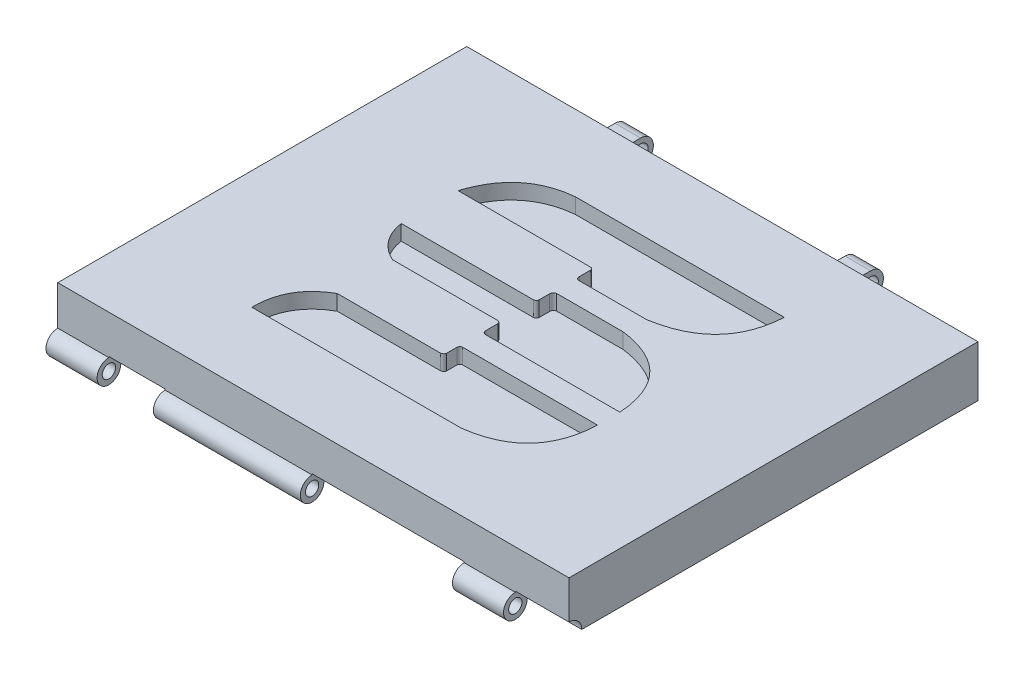
SolidWorks part; units mm, degrees
ref_plane "Front Plane" through (0, 0, 0) normal (0, 0, 1) x (1, 0, 0)
ref_plane "Top Plane" through (0, 0, 0) normal (0, 1, 0) x (1, 0, 0)
ref_plane "Right Plane" through (0, 0, 0) normal (1, 0, 0) x (0, 0, -1)
sketch "Sketch1" plane through (0, 0, 0) normal (0, 1, 0) x (1, 0, 0)
  line L0 (0, 0) -> (254, 0)
  line L1 (254, 0) -> (254, 203.2)
  line L2 (254, 203.2) -> (0, 203.2)
  line L3 (0, 203.2) -> (0, 0)
extrude "Boss-Extrude2" add sketch "Sketch1" along normal blind 12.7
sketch "Sketch2" plane through (0, 0, 0) normal (0, -1, 0) x (-1, 0, 0)
  line L1 (-254, 0) -> (-254, 203.2)
  line L2 (-254, 203.2) -> (0, 203.2)
  line L3 (0, 203.2) -> (0, 0)
  line L4 (0, 0) -> (-254, 0)
  line L6 (-12.7, 12.7) -> (-12.7, 190.5)
  line L7 (-12.7, 12.7) -> (-241.3, 12.7)
  line L8 (-241.3, 12.7) -> (-241.3, 190.5)
  line L9 (-241.3, 190.5) -> (-12.7, 190.5)
extrude "Boss-Extrude3" add sketch "Sketch2" along normal blind 12.7
sketch "Sketch3" plane through (0, 12.7, 0) normal (0, 1, 0) x (1, 0, 0)
  line L0 (-372.7889, 197.1287) -> (560.5445, 197.1287) construction
  line L1 (231.8495, 577.4485) -> (1012.5161, 577.4485) construction
  line L21 (195.367, 165.5458) -> (91.7122, 165.5458)
  line L22 (59.8464, 139.0381) -> (125.3071, 139.0381)
  line L23 (126.9605, 137.7692) -> (126.9605, 132.2725)
  line L24 (128.3037, 130.3712) -> (162.1872, 130.3712)
  line L25 (161.6423, 119.296) -> (128.4978, 119.296)
  line L26 (126.9605, 117.3978) -> (126.9605, 112.1511)
  line L27 (125.4647, 110.7847) -> (59.8464, 110.7847)
  line L28 (73.3174, 93.027) -> (125.4647, 93.027)
  line L29 (126.9605, 91.7488) -> (126.9605, 85.7448)
  line L30 (128.4978, 83.9124) -> (195.367, 83.9124)
  line L31 (195.367, 72.8024) -> (128.3037, 72.8024)
  line L32 (126.9605, 71.2973) -> (126.9605, 66.0747)
  line L33 (125.3071, 64.7692) -> (74.0829, 64.7692)
  line L34 (58.8112, 37.6226) -> (162.7167, 37.6226)
  spline S0 degree 2 poles (195.367, 165.5458) (193.7456, 135.5673) (162.1872, 130.3712) knots 0 0 0 1 1 1
  spline S1 degree 2 poles (91.7122, 165.5458) (67.5392, 163.2352) (59.8464, 139.0381) knots 0 0 0 1 1 1
  spline S2 degree 2 poles (125.3071, 139.0381) (126.7806, 139.1224) (126.9605, 137.7692) knots 0 0 0 1 1 1
  spline S3 degree 2 poles (126.9605, 132.2725) (126.8769, 130.7335) (128.3037, 130.3712) knots 0 0 0 1 1 1
  spline S4 degree 2 poles (128.4978, 119.296) (127.0701, 118.9266) (126.9605, 117.3978) knots 0 0 0 1 1 1
  spline S5 degree 2 poles (126.9605, 112.1511) (126.7438, 110.8994) (125.4647, 110.7847) knots 0 0 0 1 1 1
  spline S6 degree 2 poles (59.8464, 110.7847) (61.8873, 98.3015) (73.3174, 93.027) knots 0 0 0 1 1 1
  spline S7 degree 2 poles (125.4647, 93.027) (126.7117, 92.92) (126.9605, 91.7488) knots 0 0 0 1 1 1
  spline S8 degree 2 poles (126.9605, 85.7448) (127.0243, 84.1959) (128.4978, 83.9124) knots 0 0 0 1 1 1
  spline S9 degree 2 poles (161.6423, 119.296) (193.2226, 115.0134) (195.367, 83.9124) knots 0 0 0 1 1 1
  spline S10 degree 2 poles (128.3037, 72.8024) (127.014, 72.6481) (126.9605, 71.2973) knots 0 0 0 1 1 1
  spline S11 degree 2 poles (126.9605, 66.0747) (126.574, 64.9269) (125.3071, 64.7692) knots 0 0 0 1 1 1
  spline S12 degree 2 poles (74.0829, 64.7692) (58.4795, 55.8847) (58.8112, 37.6226) knots 0 0 0 1 1 1
  spline S13 degree 2 poles (162.7167, 37.6226) (194.1407, 41.706) (195.367, 72.8024) knots 0 0 0 1 1 1
sketch "Sketch5" plane through (0, 0, 0) normal (0, 0, 1) x (1, 0, 0)
  line L0 (254, -12.7) -> (228.6, -12.7)
  line L1 (254, -12.7) -> (0, -12.7) construction
ref_plane "Plane1" through (228.6, 0, 0) normal (1, 0, 0) x (0, 0, -1)
sketch "Sketch6" plane through (228.6, 0, 0) normal (1, 0, 0) x (0, 0, -1)
  circle A0 centre (0, -12.7) radius 6.35
extrude "Cut-Extrude2" cut sketch "Sketch6" against normal blind 52.07
sketch "Sketch7" plane through (0, 0, 0) normal (0, 0, 1) x (1, 0, 0)
  line L0 (0, -12.7) -> (25.4, -12.7)
  line L1 (176.53, -12.7) -> (0, -12.7) construction
ref_plane "Plane2" through (25.4, 0, 0) normal (-1, 0, 0) x (0, 0, 1)
sketch "Sketch8" plane through (25.4, 0, 0) normal (-1, 0, 0) x (0, 0, 1)
  circle A0 centre (0, -12.7) radius 6.35
extrude "Cut-Extrude3" cut sketch "Sketch8" against normal blind 52.07
sketch "Sketch9" plane through (228.6, 0, 0) normal (1, 0, 0) x (0, 0, -1)
  line L0 (0, -6.858) -> (0, -4.7342)
  line L1 (0, 12.7) -> (0, -12.7) construction
  line L2 (0, -4.7342) -> (6.8427, -8.9272)
  line L3 (6.8427, -8.9272) -> (6.8427, -12.7)
  line L4 (203.2, -12.7) -> (0, -12.7) construction
  line L5 (6.8427, -12.7) -> (5.842, -12.7)
  circle A0 centre (0, -12.7) radius 5.842
  circle A1 centre (0, -12.7) radius 3.302
extrude "Boss-Extrude5" add sketch "Sketch9" against normal blind 25.4 contours A0 A1 | A0 L5 L3 L2 L0
sketch "Sketch10" plane through (228.6, 0, 0) normal (1, 0, 0) x (0, 0, -1)
  circle A0 centre (0, -12.7) radius 6.35
extrude "Cut-Extrude4" cut sketch "Sketch10" along normal blind 45.212
sketch "Sketch11" plane through (176.53, 0, 0) normal (1, 0, 0) x (0, 0, -1)
  circle A0 centre (0, -12.7) radius 6.35
extrude "Cut-Extrude5" cut sketch "Sketch11" against normal blind 190.246
sketch "Sketch12" plane through (0, 0, 0) normal (-1, 0, 0) x (0, 0, 1)
  line L0 (0, -6.858) -> (0, -5.7972)
  line L1 (0, 12.7) -> (0, -6.35) construction
  line L2 (0, -5.7972) -> (-4.7292, -7.2686)
  line L3 (-4.7292, -7.2686) -> (-5.7298, -8.7792)
  line L4 (-5.7298, -8.7792) -> (-6.6519, -12.7)
  line L5 (-203.2, -12.7) -> (-6.35, -12.7) construction
  line L6 (-6.6519, -12.7) -> (-5.842, -12.7)
  circle A0 centre (0, -12.7) radius 5.842
  circle A1 centre (0, -12.7) radius 3.302
  arc M2 (-6.35, -12.7) -> (0, -6.35) centre (0, -12.7) cw
extrude "Boss-Extrude6" add sketch "Sketch12" against normal blind 24.13 contours A0 L0 L6 M2 | A0 A1
sketch "Sketch13" plane through (0, 0, 0) normal (0, 0, 1) x (1, 0, 0)
  line L0 (0, -6.858) -> (53.34, -6.858)
ref_plane "Plane3" through (53.34, 0, 0) normal (-1, 0, 0) x (0, 0, 1)
sketch "Sketch15" plane through (228.6, 0, 0) normal (1, 0, 0) x (0, 0, -1)
  circle A0 centre (0, -12.7) radius 6.35
extrude "Cut-Extrude6" cut sketch "Sketch15" against normal blind 1.27
sketch "Sketch17" plane through (203.2, 0, 0) normal (-1, 0, 0) x (0, 0, 1)
  line L0 (0, -6.858) -> (0, -4.987)
  line L1 (0, -4.987) -> (-4.743, -7.1596)
  line L2 (-4.743, -7.1596) -> (-6.563, -10.3545)
  line L3 (-6.563, -10.3545) -> (-6.563, -12.7)
  line L4 (-5.842, -12.7) -> (-203.2, -12.7) construction
  line L5 (-6.563, -12.7) -> (-5.842, -12.7)
  circle A0 centre (0, -12.7) radius 3.302
  circle A1 centre (0, -12.7) radius 5.842
  circle M1 centre (0, -12.7) radius 3.302
  line M2 (0, -6.858) -> (0, -6.35)
  arc M3 (0, -6.35) -> (-6.35, -12.7) centre (0, -12.7) ccw
  line M4 (-6.35, -12.7) -> (-5.842, -12.7)
  arc M5 (-5.842, -12.7) -> (0, -6.858) centre (0, -12.7) ccw
extrude "Boss-Extrude7" add sketch "Sketch17" along normal blind 1.27 contours A1 M2 M3 M4 | A1 M5 M1
sketch "Sketch18" plane through (24.13, 0, 0) normal (1, 0, 0) x (0, 0, -1)
  line L0 (0, -6.858) -> (0, -5.514)
  line L1 (0, -5.514) -> (4.4531, -7.4996)
  line L2 (4.4531, -7.4996) -> (6.3537, -9.9032)
  line L3 (6.3537, -9.9032) -> (6.856, -12.7)
  line L4 (6.856, -12.7) -> (5.842, -12.7)
  circle A0 centre (0, -12.7) radius 3.302
  circle A1 centre (0, -12.7) radius 5.842
  line M1 (5.842, -12.7) -> (6.35, -12.7)
  arc M2 (6.35, -12.7) -> (0, -6.35) centre (0, -12.7) ccw
  line M3 (0, -6.35) -> (0, -6.858)
  arc M4 (0, -6.858) -> (5.842, -12.7) centre (0, -12.7) ccw
  circle M5 centre (0, -12.7) radius 3.302
extrude "Boss-Extrude8" add sketch "Sketch18" along normal blind 1.27 contours A1 M1 M2 M3 | A1 M4 M5
ref_plane "Plane4" through (53.34, 0, 0) normal (-1, 0, 0) x (0, 0, 1)
sketch "Sketch19" plane through (53.34, 0, 0) normal (-1, 0, 0) x (0, 0, 1)
  line L0 (0, -6.858) -> (0, -5.3347)
  line L1 (0, 12.7) -> (0, -6.35) construction
  line L2 (0, -5.3347) -> (-5.2177, -7.6255)
  line L3 (-5.2177, -7.6255) -> (-6.5239, -10.6196)
  line L4 (-6.5239, -10.6196) -> (-6.7248, -12.7)
  line L5 (-203.2, -12.7) -> (-6.35, -12.7) construction
  line L6 (-6.7248, -12.7) -> (-5.842, -12.7)
  circle A0 centre (0, -12.7) radius 3.302
  circle A1 centre (0, -12.7) radius 5.842
extrude "Boss-Extrude9" add sketch "Sketch19" against normal blind 73.025 contours A1 L0 L2 L3 L4 L6 | A1 A0
extrude "Cut-Extrude7" cut sketch "Sketch3" against normal blind 7.62
sketch "Sketch20" plane through (0, 0, -203.2) normal (0, 0, -1) x (-1, 0, 0)
  line L0 (-254, -12.7) -> (-177.8, -12.7)
  line L1 (0, -12.7) -> (-254, -12.7) construction
ref_plane "Plane5" through (177.8, 0, 0) normal (1, 0, 0) x (0, 0, -1)
sketch "Sketch21" plane through (177.8, 0, 0) normal (1, 0, 0) x (0, 0, -1)
  line L0 (203.2, 0) -> (203.2, 6.35)
  line L1 (203.2, 12.7) -> (203.2, -12.7) construction
  line L2 (203.2, 0) -> (203.2, -6.35)
  line L3 (203.2, 6.35) -> (213.36, 6.35)
  line L4 (203.2, -6.35) -> (213.36, -6.35)
  circle A1 centre (213.36, 0) radius 6.35
extrude "Boss-Extrude10" add sketch "Sketch21" along normal blind 12.7 contours A1 L3 L0 L2 L4 | A1
sketch "Sketch22" plane through (0, 0, -203.2) normal (0, 0, -1) x (-1, 0, 0)
  line L0 (0, -12.7) -> (-76.2, -12.7)
  line L1 (0, -12.7) -> (-254, -12.7) construction
ref_plane "Plane6" through (76.2, 0, 0) normal (1, 0, 0) x (0, 0, -1)
sketch "Sketch23" plane through (76.2, 0, 0) normal (1, 0, 0) x (0, 0, -1)
  line L0 (203.2, 6.35) -> (203.2, -6.35)
  line L1 (203.2, -6.35) -> (213.36, -6.35)
  line L2 (203.2, -6.35) -> (213.36, -6.35) construction
  line L3 (203.2, 6.35) -> (213.36, 6.35)
  circle A0 centre (213.36, 0) radius 6.35
extrude "Boss-Extrude11" add sketch "Sketch23" against normal blind 12.7 contours A0 L3 L0 L1 | A0
sketch "Sketch24" plane through (63.5, 0, 0) normal (-1, 0, 0) x (0, 0, 1)
  circle A0 centre (-213.36, 0) radius 3.81
extrude "Cut-Extrude8" cut sketch "Sketch24" against normal blind 167.132
fillet "Fillet1" radius 5.08 4 edges at (184.15, -6.35, -203.2) (69.85, -6.35, -203.2) (69.85, 6.35, -203.2) (184.15, 6.35, -203.2)
